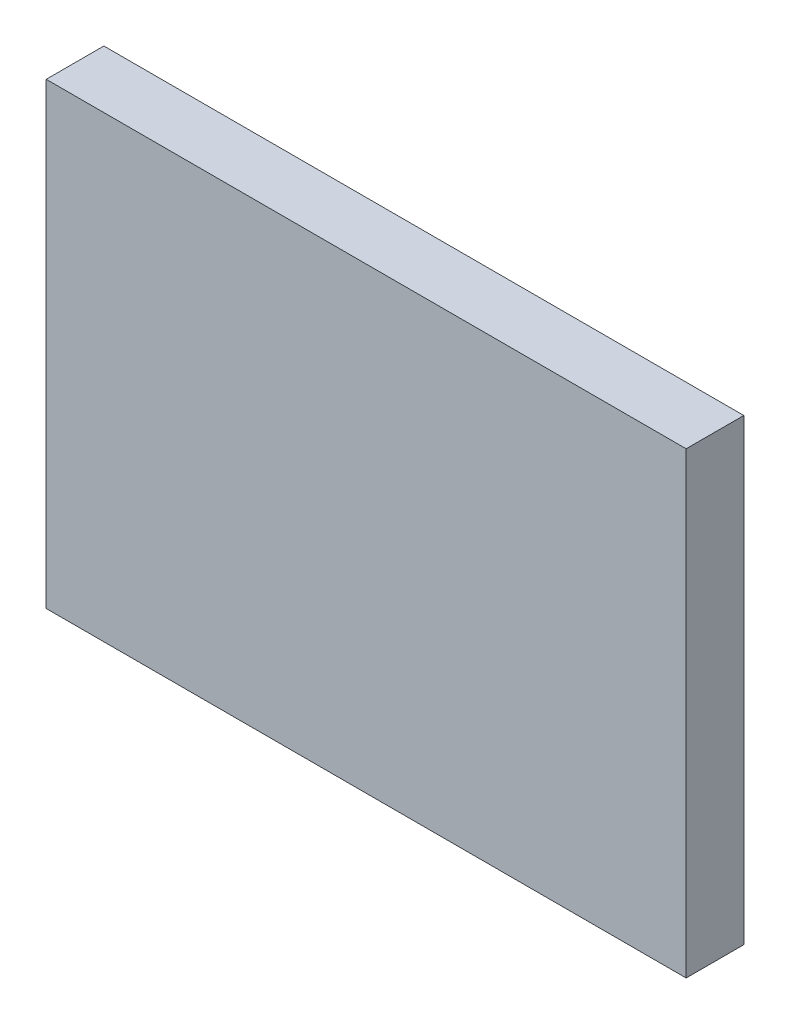
SolidWorks part; units mm, degrees
ref_plane "Front Plane" through (0, 0, 0) normal (0, 0, 1) x (1, 0, 0)
ref_plane "Top Plane" through (0, 0, 0) normal (0, 1, 0) x (1, 0, 0)
ref_plane "Right Plane" through (0, 0, 0) normal (1, 0, 0) x (0, 0, -1)
sketch "Sketch1" plane through (0, 0, 0) normal (0, 0, 1) x (1, 0, 0)
  line L1 (-23.3904, 18.0832) -> (21.0096, 18.0832)
  line L2 (-23.3904, 18.0832) -> (-23.3904, -13.7168)
  line L3 (-23.3904, -13.7168) -> (21.0096, -13.7168)
  line L4 (21.0096, 18.0832) -> (21.0096, -13.7168)
  dimension "D1" = 44.4
  dimension "D2" = 31.8
extrude "Boss-Extrude2" add sketch "Sketch1" along normal blind 4
sketch "Sketch3" plane through (0, 0, 4) normal (0, 0, 1) x (1, 0, 0)
  line L0 (-23.3904, -4.8773) -> (-8.5904, -4.8773) construction
  line L1 (-23.3904, 18.0832) -> (-23.3904, -13.7168) construction
  line L2 (21.0096, -4.8773) -> (6.2096, -4.8773) construction
  line L3 (21.0096, -13.7168) -> (21.0096, 18.0832) construction
  line L4 (-8.5904, 18.0832) -> (-8.5904, -13.7168)
  line L5 (21.0096, 18.0832) -> (-23.3904, 18.0832) construction
  line L6 (-23.3904, -13.7168) -> (21.0096, -13.7168) construction
  line L7 (6.2096, 18.0832) -> (6.2096, -13.7168)
  line L8 (-17.4602, 18.0832) -> (-17.4602, 2.1832)
  line L9 (-23.3904, 2.1832) -> (21.0096, 2.1832)
  line L10 (-23.3904, 2.1832) -> (-15.9904, 2.1832) construction
  line L11 (-8.5904, 2.1832) -> (-1.1904, 2.1832) construction
  line L12 (6.2096, 2.1832) -> (13.6096, 2.1832)
  point P25 (0, 0)
  point P26 (0, 0)
